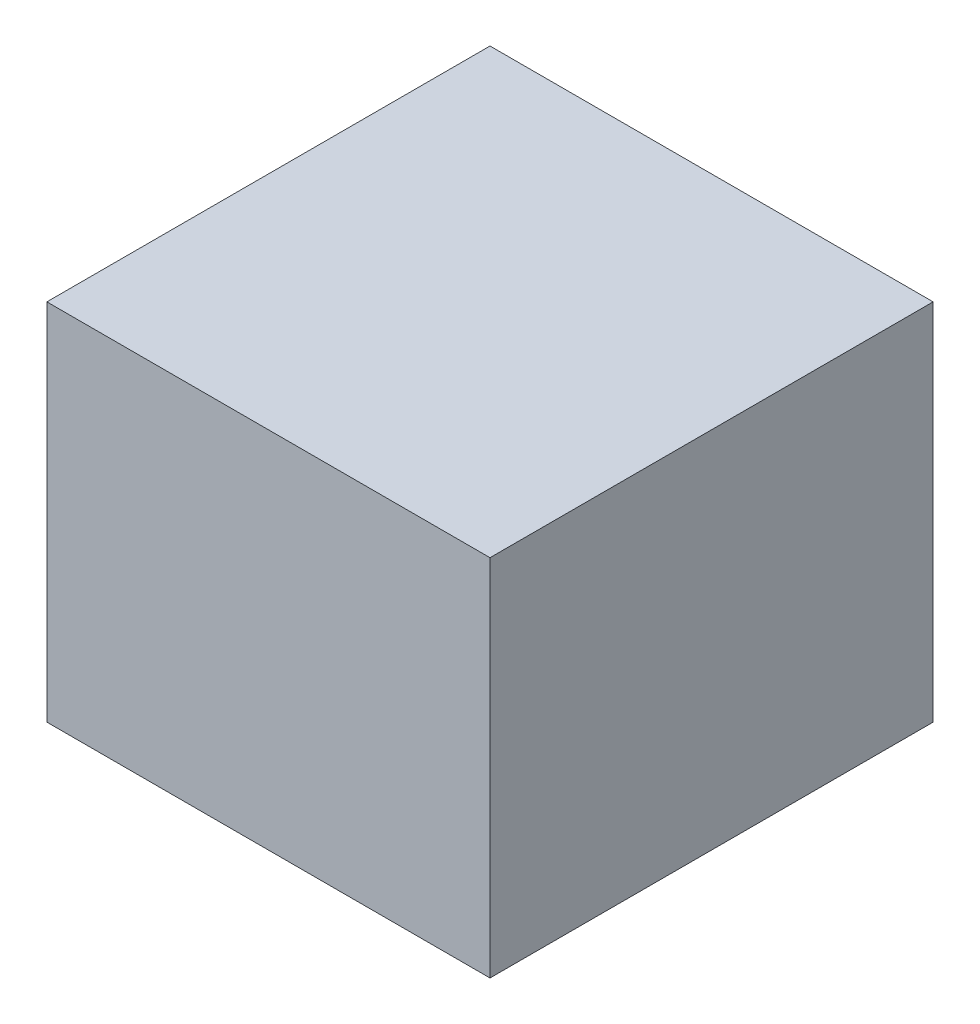
SolidWorks part; units mm, degrees
ref_plane "前视基准面" through (0, 0, 0) normal (0, 0, 1) x (1, 0, 0)
ref_plane "上视基准面" through (0, 0, 0) normal (0, 1, 0) x (1, 0, 0)
ref_plane "右视基准面" through (0, 0, 0) normal (1, 0, 0) x (0, 0, -1)
sketch "草图1" plane through (0, 0, 0) normal (0, 1, 0) x (1, 0, 0)
  line L1 (-70, 70) -> (70, 70)
  line L2 (-70, 70) -> (-70, -70)
  line L3 (-70, -70) -> (70, -70)
  line L4 (70, 70) -> (70, -70)
  line L5 (-70, 70) -> (70, -70) construction
  line L6 (-70, -70) -> (70, 70) construction
  point P0 (0, 0)
extrude "凸台-拉伸1" add sketch "草图1" along normal mid plane 115
